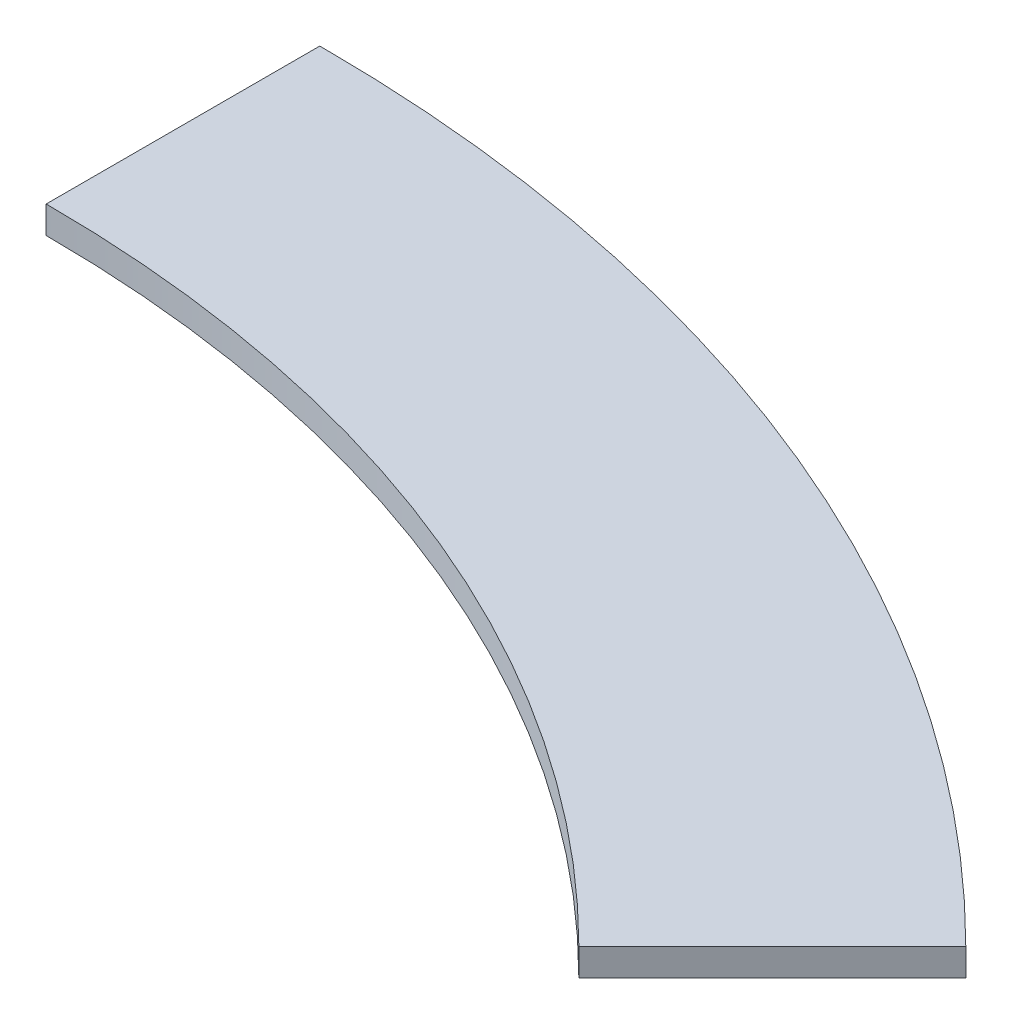
SolidWorks part; units mm, degrees
ref_plane "Front Plane" through (0, 0, 0) normal (0, 0, 1) x (1, 0, 0)
ref_plane "Top Plane" through (0, 0, 0) normal (0, 1, 0) x (1, 0, 0)
ref_plane "Right Plane" through (0, 0, 0) normal (1, 0, 0) x (0, 0, -1)
sketch "Sketch1" plane through (0, 0, 0) normal (0, 1, 0) x (1, 0, 0)
  line L0 (0, 0) -> (0, 470) construction
  line L1 (0, 470) -> (0, 570)
  line L2 (0, 0) -> (403.0509, 403.0509) construction
  line L3 (332.3402, 332.3402) -> (403.0509, 403.0509)
  arc A0 (0, 470) -> (332.3402, 332.3402) centre (0, 0) cw
  arc A1 (0, 570) -> (403.0509, 403.0509) centre (0, 0) cw
  dimension "D1" = 100
  dimension "D2" = 470
  dimension "D3" = 570
  dimension "D4" = 45
extrude "Boss-Extrude1" add sketch "Sketch1" along normal blind 10 contours A1 L1 A0 L3
